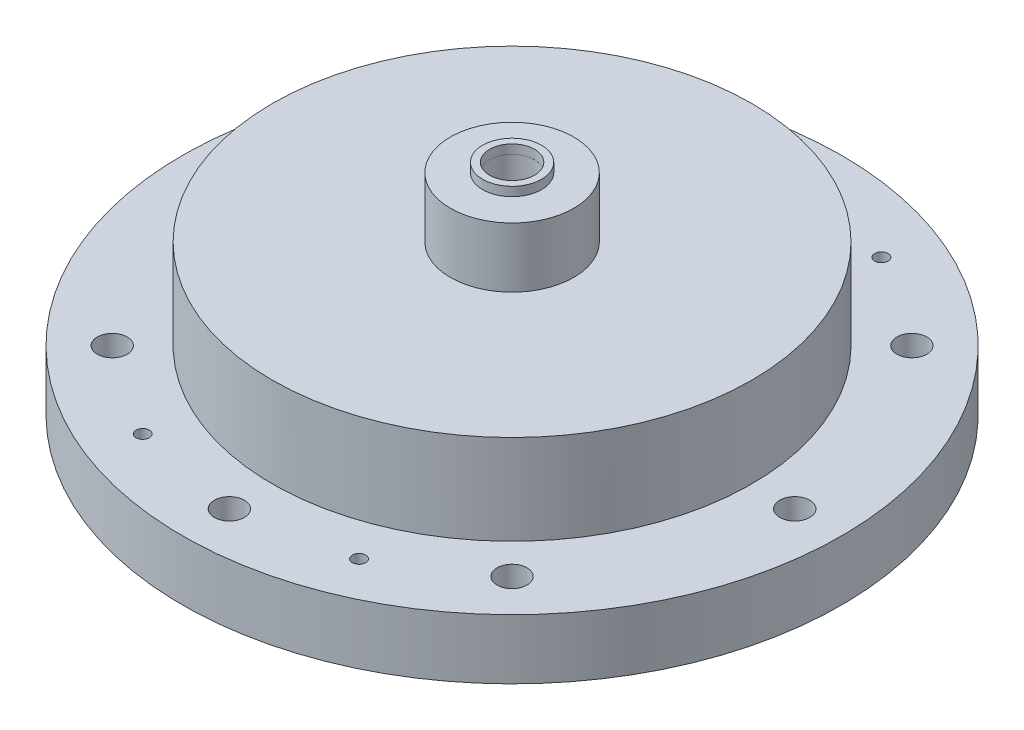
SolidWorks part; units mm, degrees
ref_plane "Front Plane" through (0, 0, 0) normal (0, 0, 1) x (1, 0, 0)
ref_plane "Top Plane" through (0, 0, 0) normal (0, 1, 0) x (1, 0, 0)
ref_plane "Right Plane" through (0, 0, 0) normal (1, 0, 0) x (0, 0, -1)
sketch "Sketch1" plane through (0, 0, 0) normal (0, 1, 0) x (1, 0, 0)
  circle A1 centre (0, 0) radius 50.8
  dimension "D1" = 101.6
extrude "Boss-Extrude1" add sketch "Sketch1" along normal blind 25.4
sketch "Sketch2" plane through (0, 0, 0) normal (0, -1, 0) x (1, 0, 0)
  circle A0 centre (0, 0) radius 50.8
  circle A1 centre (0, 0) radius 69.85
  dimension "D1" = 139.7
extrude "Boss-Extrude2" add sketch "Sketch2" against normal blind 12.7
sketch "Sketch4" plane through (0, 0, 0) normal (0, -1, 0) x (1, 0, 0)
  circle A0 centre (0, -59.9186) radius 3.175
  circle A1 centre (-42.3688, -42.3688) radius 3.175
  circle A2 centre (-59.9186, 0) radius 3.175
  circle A3 centre (-42.3688, 42.3688) radius 3.175
  circle A4 centre (0, 59.9186) radius 3.175
  circle A5 centre (42.3688, 42.3688) radius 3.175
  circle A6 centre (59.9186, 0) radius 3.175
  circle A7 centre (42.3688, -42.3688) radius 3.175
  point P35 (0, 0)
  dimension "D2" = 6.35
  dimension "D1" = 59.9186
  dimension "D3" = 8
extrude "Cut-Extrude2" cut sketch "Sketch4" against normal up to next
sketch "Sketch5" plane through (0, 25.4, 0) normal (0, 1, 0) x (1, 0, 0)
  circle A0 centre (0, 0) radius 12.827
  dimension "D1" = 25.654
extrude "Cut-Extrude3" cut sketch "Sketch5" against normal blind 19.05 from offset 0
sketch "Sketch6" plane through (0, 6.35, 0) normal (0, 1, 0) x (1, 0, 0)
  circle A0 centre (0, 0) radius 1.5875
  dimension "D1" = 3.175
extrude "Cut-Extrude4" cut sketch "Sketch6" against normal up to next
sketch "Sketch34" plane through (0, 25.4, 0) normal (0, 1, 0) x (1, 0, 0)
  circle A0 centre (0, 0) radius 13.081
  circle A1 centre (0, 0) radius 4.7625
  dimension "D1" = 26.162
  dimension "D2" = 9.525
extrude "Boss-Extrude3" add sketch "Sketch34" along normal blind 19.05
cosmetic thread "Cosmetic Thread4" parameters "D2"=23.1953
sketch "Sketch40" plane through (0, 25.4, 0) normal (0, 1, 0) x (1, 0, 0)
  circle A0 centre (0, 0) radius 50.8
extrude "Boss-Extrude5" add sketch "Sketch40" along normal blind 6.35
sketch "Sketch38" plane through (0, 44.45, 0) normal (0, 1, 0) x (1, 0, 0)
  circle A0 centre (0, 0) radius 6.2484
  dimension "D1" = 12.4968
extrude "Boss-Extrude4" add sketch "Sketch38" along normal blind 1.905 separate body
sketch "Sketch39" plane through (0, 46.355, 0) normal (0, 1, 0) x (1, 0, 0)
  circle A0 centre (0, 0) radius 4.7625
  dimension "D1" = 9.525
extrude "Cut-Extrude7" cut sketch "Sketch39" against normal blind 50.8
sketch "Sketch41" plane through (0, 31.75, 0) normal (0, 1, 0) x (1, 0, 0)
  circle A0 centre (0, 0) radius 4.7625
  dimension "D1" = 9.525
extrude "Cut-Extrude8" cut sketch "Sketch41" against normal blind 6.35
sketch "Sketch42" plane through (0, 0, 0) normal (0, -1, 0) x (1, 0, 0)
  circle A0 centre (0, 0) radius 23.7871
  dimension "D1" = 47.5742
extrude "Cut-Extrude9" [suppressed] cut sketch "Sketch42" against normal blind 6.477
hole_wizard "#10-24 Tapped Hole1" [suppressed] positions "Sketch44" profile "Sketch45" tap size "#10-24" standard "ANSI Inch"
sketch "Sketch44" [suppressed] plane through (0, 6.477, 0) normal (0, -1, 0) x (-1, 0, 0)
  line L0 (0, 0) -> (0, -35.56) construction
  line L2 (0, 0) -> (0, 30.48) construction
  line L4 (0, 0) -> (-27.94, 0) construction
  line L6 (0, 0) -> (30.48, 0) construction
  circle A0 centre (0, 0) radius 17.4625 construction
  point P0 (0, -17.4625)
  point P2 (-17.4625, 0)
  point P4 (0, 17.4625)
  point P6 (17.4625, 0)
  dimension "D1" = 34.925
sketch "Sketch45" plane through (0, 6.477, 17.4625) normal (1, 0, 0) x (0, 0, -1)
  line L0 (0, 0) -> (0, 13.8408)
  line L1 (0, 13.8408) -> (1.8986, 12.7)
  line L2 (1.8986, 12.7) -> (1.8986, 0)
  line L5 (1.8986, 0) -> (0, 0)
  line L10 (0, 13.8408) -> (-1.8987, 12.7) construction
  line L11 (0, -6.35) -> (0, 107.95) construction
  dimension "Tap Drill Dia." = 3.7973
  dimension "Tap Drill Depth" = 12.7
  dimension "Drill Angle" = 118
cosmetic thread "Hole Thread1" parameters "D1"=9.652, "D2"=4.826
cosmetic thread "Hole Thread2" parameters "D1"=9.652, "D2"=4.826
cosmetic thread "Hole Thread3" parameters "D1"=9.652, "D2"=4.826
cosmetic thread "Hole Thread4" parameters "D1"=9.652, "D2"=4.826
sketch "Sketch46" plane through (0, 0, 0) normal (0, -1, 0) x (1, 0, 0)
  line L0 (0, -83.82) -> (0, 83.82) construction
  line L1 (34.3522, -82.9336) -> (-34.3522, 82.9336) construction
  line L2 (-32.8909, -79.4057) -> (32.8909, 79.4057) construction
  circle A0 centre (0, 0) radius 59.9186 construction
  circle A1 centre (-22.9299, 55.3576) radius 3.175
  circle A2 centre (22.9299, 55.3576) radius 3.175
  circle A3 centre (-22.9299, -55.3576) radius 3.175
  circle A4 centre (22.9299, -55.3576) radius 3.175
  point P7 (0, 0)
  point P10 (0, 0)
  point P12 (0, 0)
  dimension "D1" = 119.8372
  dimension "D4" = 6.35
  dimension "D5" = 6.35
  dimension "D6" = 6.35
  dimension "D7" = 6.35
  dimension "D2" = 22.5
  dimension "D3" = 22.5
extrude "Cut-Extrude10" cut sketch "Sketch46" against normal blind 6.35
hole_wizard "1/4-20 Tapped Hole1" [suppressed] positions "Sketch47" profile "Sketch48" tap size "1/4-20" standard "ANSI Inch"
sketch "Sketch47" plane through (0, 31.75, 0) normal (0, 1, 0) x (1, 0, 0)
  line L0 (0, 0) -> (0, 45.3569) construction
  line L2 (0, 0) -> (-40.0078, -23.0985) construction
  line L4 (0, 0) -> (38.662, -22.3215) construction
  circle A0 centre (0, 0) radius 38.1 construction
  point P0 (0, 38.1)
  point P2 (32.9956, -19.05)
  point P4 (-32.9956, -19.05)
  dimension "D1" = 76.2
  dimension "D2" = 120
  dimension "D3" = 120
sketch "Sketch48" plane through (0, 31.75, -38.1) normal (1, 0, 0) x (0, 0, 1)
  line L0 (0, 0) -> (0, 15.5038)
  line L1 (0, 15.5038) -> (2.5527, 13.97)
  line L2 (2.5527, 13.97) -> (2.5527, 0)
  line L5 (2.5527, 0) -> (0, 0)
  line L10 (0, 15.5038) -> (-2.5527, 13.97) construction
  line L11 (0, -6.35) -> (0, 107.95) construction
  dimension "Tap Drill Dia." = 5.1054
  dimension "Tap Drill Depth" = 13.97
  dimension "Drill Angle" = 118
cosmetic thread "Hole Thread5" [suppressed] parameters "D1"=12.7, "D2"=6.35
cosmetic thread "Hole Thread6" [suppressed] parameters "D1"=12.7, "D2"=6.35
cosmetic thread "Hole Thread7" [suppressed] parameters "D1"=12.7, "D2"=6.35
sketch "Sketch49" [suppressed] plane through (0, 6.477, 0) normal (0, -1, 0) x (1, 0, 0)
  circle A0 centre (0, 0) radius 23.8252
  dimension "D1" = 47.6504
extrude "Cut-Extrude11" cut sketch "Sketch49" against normal blind 3.937 from surface at 6.477 starting at face at (22.9299, 0, 52.1826)
sketch "Sketch50" plane through (0, 6.35, 0) normal (0, -1, 0) x (1, 0, 0)
  circle A0 centre (-22.9299, 55.3576) radius 1.4097
  circle A1 centre (22.9299, 55.3576) radius 1.4097
  circle A2 centre (-22.9299, -55.3576) radius 1.4097
  circle A3 centre (22.9299, -55.3576) radius 1.4097
  dimension "D1" = 2.8194
  dimension "D2" = 2.8194
  dimension "D3" = 2.8194
  dimension "D4" = 2.8194
extrude "Cut-Extrude12" cut sketch "Sketch50" against normal through all
sketch "Sketch51" plane through (0, 0, 0) normal (0, -1, 0) x (1, 0, 0)
  circle A0 centre (0, 0) radius 44.45
extrude "Cut-Extrude13" cut sketch "Sketch51" against normal blind 25.4
sketch "Sketch52" plane through (0, 0, 0) normal (0, -1, 0) x (-1, 0, 0)
  circle A0 centre (0, 0) radius 4.7625
  circle A1 centre (0, 0) radius 44.45
  dimension "D1" = 9.525
extrude "Boss-Extrude6" add sketch "Sketch52" against normal blind 25.4
